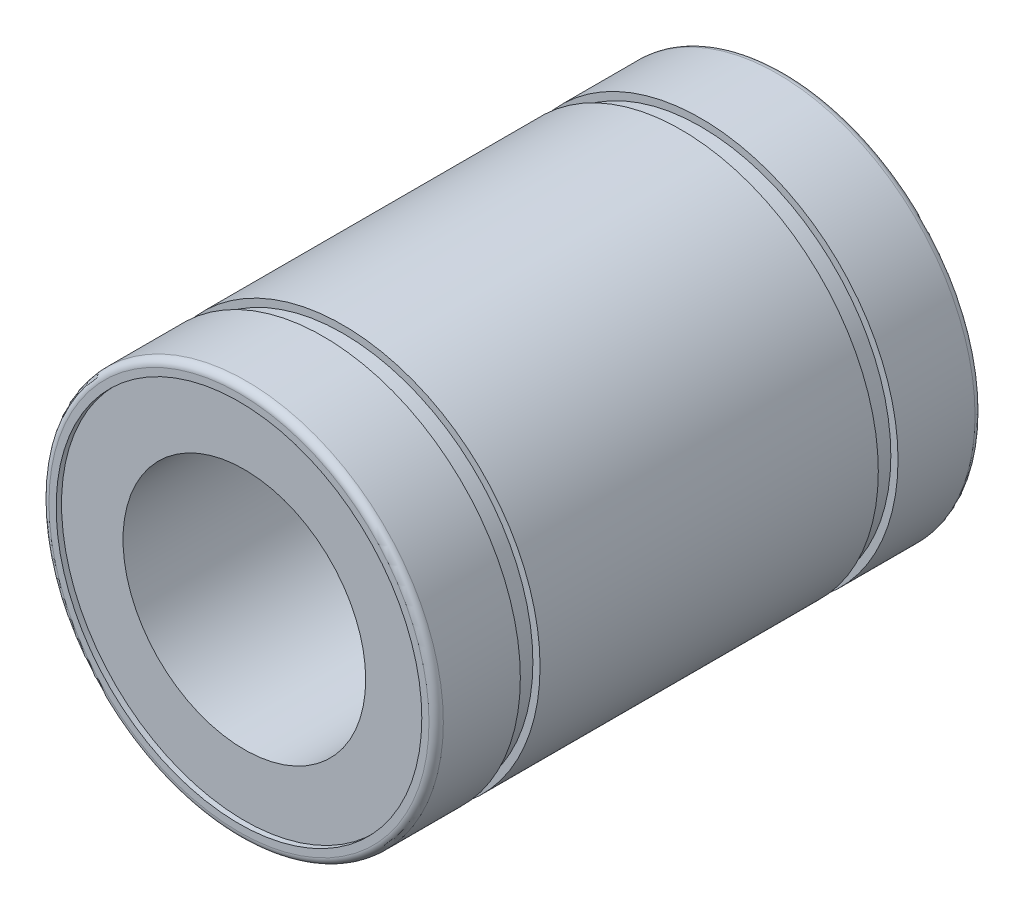
SolidWorks part; units mm, degrees
ref_plane "Front" through (0, 0, 0) normal (0, 0, 1) x (1, 0, 0)
ref_plane "Top" through (0, 0, 0) normal (0, 1, 0) x (1, 0, 0)
ref_plane "Right" through (0, 0, 0) normal (1, 0, 0) x (0, 0, -1)
sketch "Support-Right" plane through (0, 0, 0) normal (1, 0, 0) x (0, 0, -1)
  line L0 (-18, 0) -> (18, 0) construction
  line L1 (-17.6453, 8) -> (17.6453, 8)
  line L2 (17.6453, 8) -> (17.6453, 12.0537)
  line L3 (17.6453, 12.0537) -> (18, 12.0537)
  line L4 (18, 12.0537) -> (18, 12.5268)
  line L5 (17.5268, 13) -> (-17.5268, 13)
  line L6 (11.15, 13) -> (11.15, 12.5268)
  line L7 (-11.15, 13) -> (-11.15, 12.5268)
  line L8 (11.15, 12.5268) -> (12.45, 12.5268)
  line L9 (-11.15, 12.5268) -> (-12.45, 12.5268)
  line L10 (0, 0) -> (0, 13) construction
  line L11 (12.45, 12.5268) -> (12.45, 13)
  line L12 (-12.45, 12.5268) -> (-12.45, 13)
  line L13 (-17.6453, -8) -> (-17.6453, -12.0537)
  line L14 (-17.6453, -12.0537) -> (-18, -12.0537)
  line L15 (-18, 12.0537) -> (-18, 12.5268)
  line L16 (-17.6453, 12.0537) -> (-18, 12.0537)
  line L17 (-17.6453, 8) -> (-17.6453, 12.0537)
  line L18 (17.5268, 12.5268) -> (17.5268, 13) construction
  line L19 (-18, -12.0537) -> (-18, -12.5268)
  line L20 (-12.45, -12.5268) -> (-12.45, -13)
  line L21 (12.45, -12.5268) -> (12.45, -13)
  line L22 (-11.15, -12.5268) -> (-12.45, -12.5268)
  line L23 (11.15, -12.5268) -> (12.45, -12.5268)
  line L24 (-11.15, -13) -> (-11.15, -12.5268)
  line L25 (11.15, -13) -> (11.15, -12.5268)
  line L26 (17.5268, -13) -> (-17.5268, -13)
  line L27 (18, -12.0537) -> (18, -12.5268)
  line L28 (17.6453, -12.0537) -> (18, -12.0537)
  line L29 (17.6453, -8) -> (17.6453, -12.0537)
  line L30 (-17.6453, -8) -> (17.6453, -8)
  line L31 (17.6453, 8) -> (18, 12.0537) construction
  line L32 (11.15, 12.5268) -> (12.45, 13) construction
  arc A0 (18, 12.5268) -> (17.5268, 13) centre (17.5268, 12.5268) ccw
  arc A1 (-18, 12.5268) -> (-17.5268, 13) centre (-17.5268, 12.5268) cw
  arc A2 (-18, -12.5268) -> (-17.5268, -13) centre (-17.5268, -12.5268) ccw
  arc A3 (18, -12.5268) -> (17.5268, -13) centre (17.5268, -12.5268) cw
  dimension "D1" = 5
  dimension "Width-Track" = 1.3
  dimension "Dist-Track" = 24.9
  dimension "Diam-Shaft" = 16
  dimension "Length-Ball-Bearing" = 36
  dimension "Diam-Ball-Bearing" = 26
  dimension "D2" = 20
sketch "Sketch2" plane through (0, 0, 0) normal (1, 0, 0) x (0, 0, -1)
  line L0 (-17.6453, 12.0537) -> (-18, 12.0537) construction
  line L1 (17.6453, 12.0537) -> (18, 12.0537) construction
  line L2 (-18, 12.0537) -> (-18, 12.5268) construction
  line L3 (17.6453, 8) -> (17.6453, 12.0537) construction
  line L4 (18, 12.0537) -> (18, 12.5268) construction
  line L5 (17.5268, 13) -> (-17.5268, 13) construction
  line L6 (-17.6453, 8) -> (-17.6453, 12.0537) construction
  line L7 (-17.6453, 8) -> (17.6453, 8) construction
  line L8 (-18, 0) -> (18, 0) construction
  line L9 (-17.6453, 12.0537) -> (-18, 12.0537)
  line L10 (17.6453, 12.0537) -> (18, 12.0537)
  line L11 (-18, 12.0537) -> (-18, 12.5268)
  line L12 (17.6453, 8) -> (17.6453, 12.0537)
  line L13 (18, 12.0537) -> (18, 12.5268)
  line L14 (17.5268, 13) -> (-17.5268, 13)
  line L15 (-17.6453, 8) -> (-17.6453, 12.0537)
  line L16 (-17.6453, 8) -> (17.6453, 8)
  line L17 (-18, 0) -> (18, 0) construction
  arc A0 (-17.5268, 13) -> (-18, 12.5268) centre (-17.5268, 12.5268) ccw construction
  arc A1 (18, 12.5268) -> (17.5268, 13) centre (17.5268, 12.5268) ccw construction
  arc A2 (-17.5268, 13) -> (-18, 12.5268) centre (-17.5268, 12.5268) ccw
  arc A3 (18, 12.5268) -> (17.5268, 13) centre (17.5268, 12.5268) ccw
revolve "Body" add sketch "Sketch2" angle 360 about L17
sketch "Sketch3" plane through (0, 0, 0) normal (1, 0, 0) x (0, 0, -1)
  line L0 (12.45, 12.5268) -> (12.45, 13) construction
  line L1 (11.15, 12.5268) -> (12.45, 12.5268) construction
  line L2 (11.15, 13) -> (11.15, 12.5268) construction
  line L3 (-11.15, 13) -> (-11.15, 12.5268) construction
  line L4 (-11.15, 12.5268) -> (-12.45, 12.5268) construction
  line L5 (-12.45, 12.5268) -> (-12.45, 13) construction
  line L6 (-18, 0) -> (18, 0) construction
  line L7 (12.45, 12.5268) -> (12.45, 13)
  line L8 (11.15, 12.5268) -> (12.45, 12.5268)
  line L9 (11.15, 13) -> (11.15, 12.5268)
  line L10 (-11.15, 13) -> (-11.15, 12.5268)
  line L11 (-11.15, 12.5268) -> (-12.45, 12.5268)
  line L12 (-12.45, 12.5268) -> (-12.45, 13)
  line L13 (-18, 0) -> (18, 0) construction
  line L14 (-12.45, 13) -> (-11.15, 13)
  line L15 (11.15, 13) -> (12.45, 13)
revolve "Track" cut sketch "Sketch3" angle 360 about L13
sketch "Sketch4" plane through (0, 0, 0) normal (1, 0, 0) x (0, 0, -1)
  line L0 (11.15, 13) -> (11.15, 12.5268) construction
  line L1 (-11.15, 13) -> (-11.15, 12.5268) construction
  line L2 (11.15, 13) -> (11.15, 12.7634)
  line L3 (-11.15, 13) -> (-11.15, 12.7634)
  line L4 (-11.15, 12.7634) -> (11.15, 12.7634)
  line L5 (-11.15, 13) -> (11.15, 13)
  line L6 (-18, 0) -> (18, 0) construction
  line L7 (-18, 0) -> (18, 0) construction
revolve "Cosmetic-Cut" [suppressed] cut sketch "Sketch4" angle 20 about L7
pattern_circular "Pattern-Cosmetic-Cut" [suppressed] count 5 over 360 about axis through (0, 0, 18) along (0, 0, -1)
